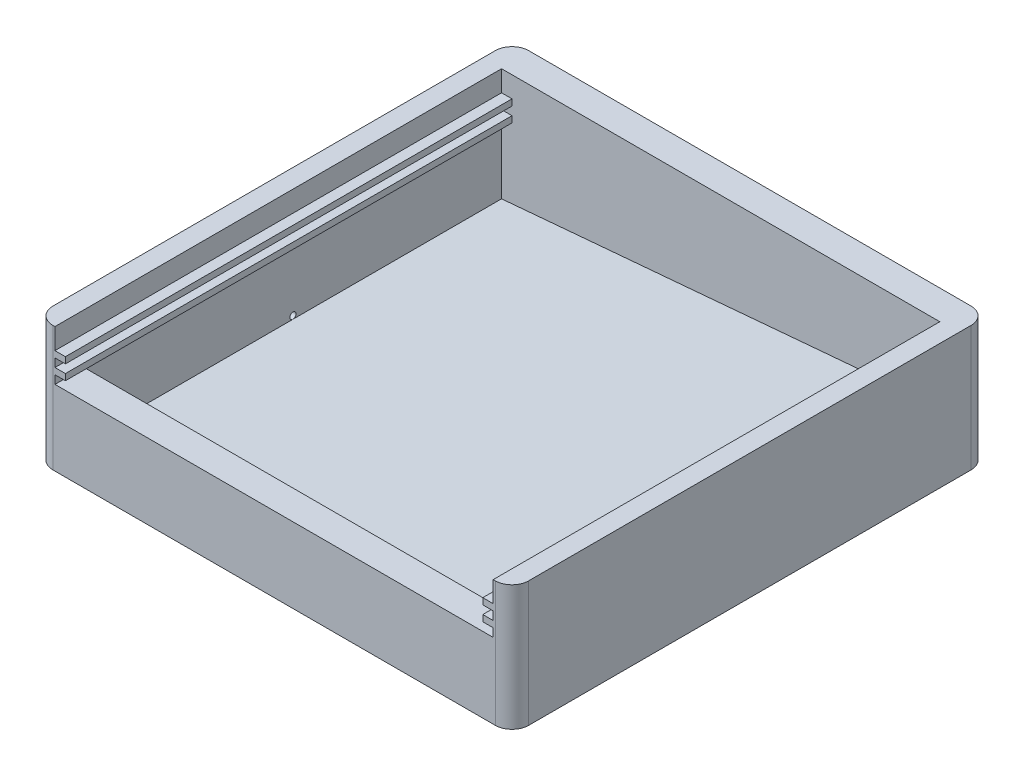
SolidWorks part; units mm, degrees
ref_plane "Alzado" through (0, 0, 0) normal (0, 0, 1) x (1, 0, 0)
ref_plane "Planta" through (0, 0, 0) normal (0, 1, 0) x (1, 0, 0)
ref_plane "Vista lateral" through (0, 0, 0) normal (1, 0, 0) x (0, 0, -1)
sketch "Croquis1" plane through (0, 0, 0) normal (0, 1, 0) x (1, 0, 0)
  line L1 (-57, -57) -> (57, -57)
  line L2 (-57, -57) -> (-57, 57)
  line L3 (-57, 57) -> (57, 57)
  line L4 (57, -57) -> (57, 57)
  line L5 (-57, -57) -> (57, 57) construction
  line L6 (-57, 57) -> (57, -57) construction
  point P0 (0, 0)
  dimension "D1" = 114
  dimension "D2" = 114
extrude "Saliente-Extruir1" add sketch "Croquis1" along normal blind 30
fillet "Redondeo1" radius 4 4 edges at (-57, 15, -57) (-57, 15, 57) (57, 15, -57) (57, 15, 57)
sketch "Croquis2" plane through (0, 30, 0) normal (0, 1, 0) x (1, 0, 0)
  line L1 (-52.5, -50) -> (52.5, -50)
  line L2 (-52.5, -50) -> (-52.5, 50)
  line L3 (-52.5, 50) -> (52.5, 50)
  line L4 (52.5, -50) -> (52.5, 50)
  line L5 (-52.5, -50) -> (52.5, 50) construction
  line L6 (-52.5, 50) -> (52.5, -50) construction
  point P0 (0, 0)
  dimension "D1" = 100
  dimension "D2" = 105
extrude "Cortar-Extruir1" cut sketch "Croquis2" against normal blind 27
sketch "Croquis3" plane through (0, 0, 57) normal (0, 0, 1) x (1, 0, 0)
  line L0 (-53, 30) -> (53, 30) construction
  line L1 (-52.5, 18) -> (52.5, 18)
  line L2 (-52.5, 18) -> (-52.5, 30)
  line L3 (-52.5, 30) -> (52.5, 30)
  line L4 (52.5, 18) -> (52.5, 30)
  line L5 (-52.5, 18) -> (52.5, 30) construction
  line L6 (-52.5, 30) -> (52.5, 18) construction
  point P0 (0, 24)
  dimension "D1" = 105
  dimension "D2" = 12
extrude "Cortar-Extruir2" cut sketch "Croquis3" against normal up to surface (7 mm away) up to face at (0, 16.5, 50)
sketch "Croquis5" plane through (0, 0, 57) normal (0, 0, 1) x (1, 0, 0)
  line L0 (-52.5, 30) -> (-52.5, 18) construction
  line L1 (-52.5, 20) -> (-50, 20)
  line L2 (-52.5, 20) -> (-52.5, 21.5)
  line L3 (-52.5, 21.5) -> (-50, 21.5)
  line L4 (-50, 20) -> (-50, 21.5)
  line L5 (-52.5, 18) -> (52.5, 18) construction
  line L6 (0, 0) -> (0, 18) construction
  line L7 (-52.5, 18) -> (52.5, 18) construction
  line L12 (-52.5, 3) -> (-52.5, 30) construction
  line L13 (-52.5, 25) -> (-50, 25)
  line L14 (-52.5, 25) -> (-52.5, 23.5)
  line L15 (-52.5, 23.5) -> (-50, 23.5)
  line L16 (-50, 25) -> (-50, 23.5)
  line L17 (52.5, 21.5) -> (50, 21.5)
  line L18 (50, 20) -> (50, 21.5)
  line L19 (52.5, 20) -> (50, 20)
  line L20 (52.5, 20) -> (52.5, 21.5)
  line L21 (52.5, 23.5) -> (50, 23.5)
  line L22 (50, 25) -> (50, 23.5)
  line L23 (52.5, 25) -> (50, 25)
  line L24 (52.5, 25) -> (52.5, 23.5)
  dimension "D1" = 1.5
  dimension "D2" = 2.5
  dimension "D3" = 2
  dimension "D4" = 2
  dimension "D5" = 2.5
  dimension "D6" = 1.5
extrude "Saliente-Extruir2" add sketch "Croquis5" against normal up to surface (107 mm away) up to face at (0, 16.5, -50)
sketch "Croquis6" plane through (0, 0, 0) normal (0, 0, 1) x (1, 0, 0)
  line L0 (-52.5, 3) -> (52.5, 12.1863)
  line L1 (52.5, 3) -> (52.5, 20) construction
  line L2 (52.5, 12.1863) -> (52.5, 3)
  line L3 (52.5, 3) -> (-52.5, 3)
  dimension "D1" = 5
extrude "Saliente-Extruir3" add sketch "Croquis6" against normal up to surface and the other way up to surface up to face at (0, 21.3, -50) other way up to face at (0, 10.5, 50)
sketch "Croquis7" plane through (-57, 0, 0) normal (-1, 0, 0) x (0, 0, 1)
  circle A0 centre (0, 3.75) radius 0.75
  point P2 (0, 0)
  dimension "D2" = 1.5
  dimension "D1" = 3.75
extrude "Cortar-Extruir3" cut sketch "Croquis7" against normal up to surface (4.5 mm away) up to face at (-52.5, 27.5, 3.5)
sketch "Croquis9" plane through (-57, 0, 0) normal (-1, 0, 0) x (0, 0, 1)
  point P0 (0, 3.75)
sketch "Croquis10" plane through (0, 0, 0) normal (0, 0, 1) x (1, 0, 0)
  line L0 (-57, 3) -> (-62, 3)
  line L1 (-62, 3) -> (-62, 2.75)
  line L2 (-62, 2.75) -> (-59, 2.2)
  line L3 (-59, 2.2) -> (-59, 2.45)
  line L4 (-59, 2.45) -> (-57, 2.45)
  line L5 (-57, 0) -> (-57, 30) construction
  line L6 (-57, 2.45) -> (-57, 3)
  line L7 (-57, 3.75) -> (-53, 3.75) construction
  line L8 (-53, 30) -> (-53, 0) construction
  dimension "D1" = 5
  dimension "D2" = 1
  dimension "D3" = 1.3
  dimension "D4" = 1.55
  dimension "D5" = 2
revolve "Revolución1" add sketch "Croquis10" angle 360 about L7
